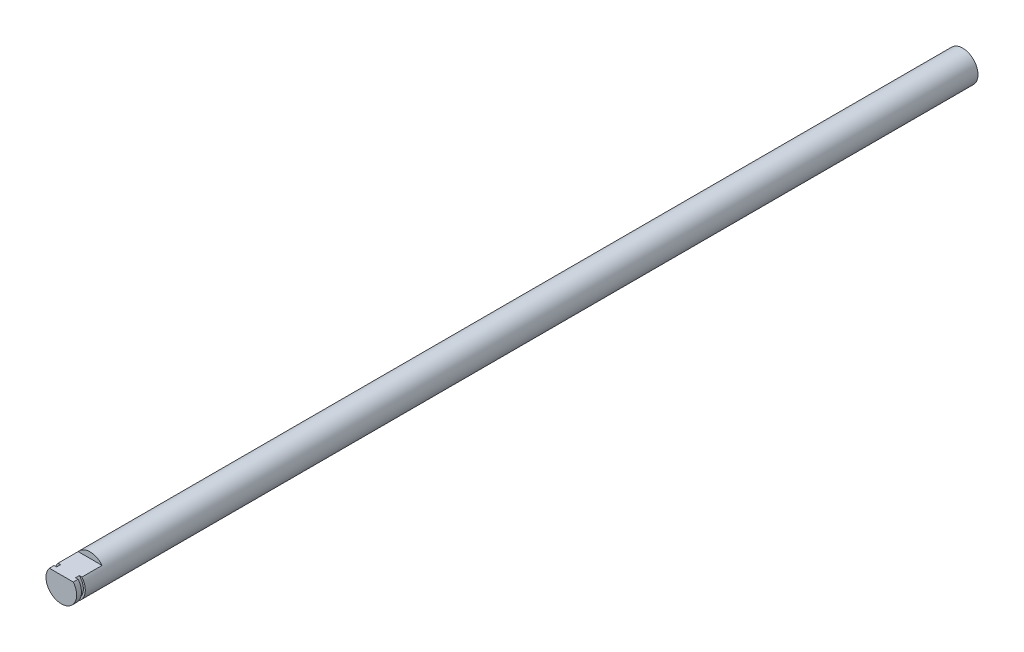
SolidWorks part; units mm, degrees
ref_plane "Front Plane" through (0, 0, 0) normal (0, 0, 1) x (1, 0, 0)
ref_plane "Top Plane" through (0, 0, 0) normal (0, 1, 0) x (1, 0, 0)
ref_plane "Right Plane" through (0, 0, 0) normal (1, 0, 0) x (0, 0, -1)
sketch "Sketch1" plane through (0, 0, 0) normal (0, 0, 1) x (1, 0, 0)
  circle A0 centre (0, 0) radius 4
  dimension "D1" = 8
extrude "Boss-Extrude1" add sketch "Sketch1" along normal blind 235
sketch "Sketch2" plane through (0, 0, 235) normal (0, 0, 1) x (1, 0, 0)
  line L0 (3.1225, 2.5) -> (-3.1225, 2.5)
  circle A1 centre (0, 0) radius 4
  arc A2 (3.1225, 2.5) -> (-3.1225, 2.5) centre (0, 0) ccw
  dimension "D2" = 2.5
  dimension "D1" = 0
extrude "Cut-Extrude1" cut sketch "Sketch2" against normal blind 7.5
ref_plane "Plane1" through (0, 0, 233.75) normal (0, 0, 1) x (1, 0, 0)
sketch "Sketch3" plane through (0, 0, 233.75) normal (0, 0, 1) x (1, 0, 0)
  circle A0 centre (0, 0) radius 4
  circle A1 centre (0, 0) radius 3.5
extrude "Cut-Extrude2" cut sketch "Sketch3" against normal blind 1
